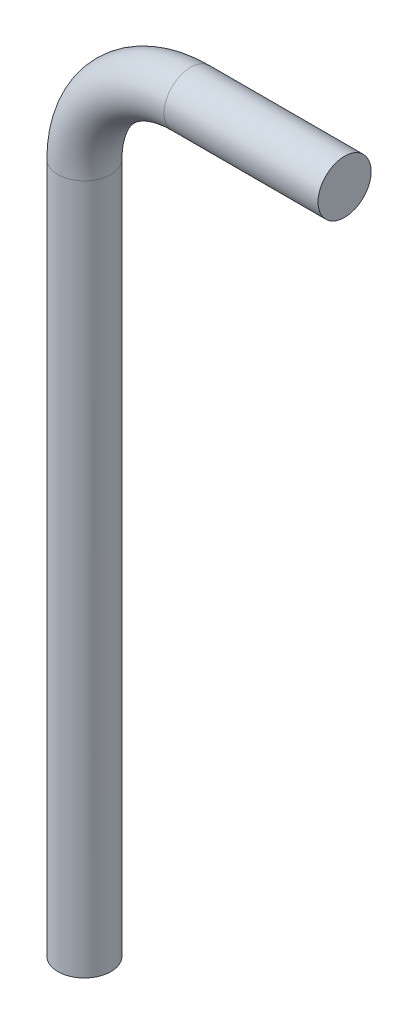
SolidWorks part; units mm, degrees
ref_plane "Front Plane" through (0, 0, 0) normal (0, 0, 1) x (1, 0, 0)
ref_plane "Top Plane" through (0, 0, 0) normal (0, 1, 0) x (1, 0, 0)
ref_plane "Right Plane" through (0, 0, 0) normal (1, 0, 0) x (0, 0, -1)
sketch "Sketch3" plane through (0, 0, 0) normal (0, 1, 0) x (1, 0, 0)
  circle A0 centre (0, 0) radius 2.5
sketch "Sketch5" plane through (0, 0, 0) normal (0, 0, 1) x (1, 0, 0)
  line L0 (0, 0) -> (0, 65)
  line L1 (24.4975, 75) -> (10, 75)
  arc A0 (10, 75) -> (0, 65) centre (10, 65) ccw
  dimension "D1" = 10
sweep "Sweep2" add profiles "Sketch3" path "Sketch5"
